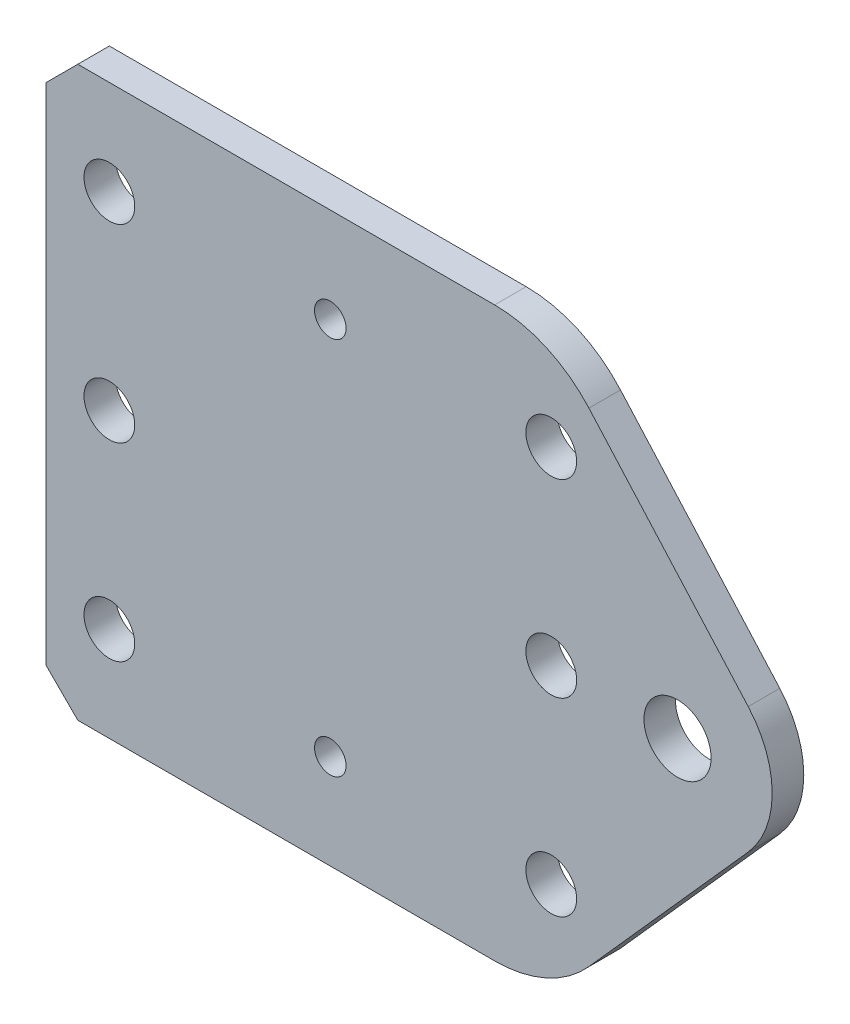
SolidWorks part; units mm, degrees
material "6061-T6 (SS)"
ref_plane "Front Plane" through (0, 0, 0) normal (0, 0, 1) x (1, 0, 0)
ref_plane "Top Plane" through (0, 0, 0) normal (0, 1, 0) x (1, 0, 0)
ref_plane "Right Plane" through (0, 0, 0) normal (1, 0, 0) x (0, 0, -1)
sketch "Sketch1" plane through (0, 0, 0) normal (0, 0, 1) x (1, 0, 0)
  line L0 (0, 0) -> (45.1053, 0)
  line L1 (54.5881, 4.2521) -> (70.6121, 22.2391)
  line L2 (70.6121, 34.9109) -> (54.5881, 52.8979)
  line L3 (45.1053, 57.15) -> (0, 57.15)
  line L4 (0, 57.15) -> (0, 0)
  arc A0 (70.6121, 22.2391) -> (70.6121, 34.9109) centre (63.5, 28.575) ccw
  circle A1 centre (63.5, 28.575) radius 3.3782
  arc A2 (45.1053, 0) -> (54.5881, 4.2521) centre (45.1053, 12.7) ccw
  arc A3 (54.5881, 52.8979) -> (45.1053, 57.15) centre (45.1053, 44.45) ccw
  point P11 (50.8, 0)
  dimension "D3" = 12.7
  dimension "D4" = 9.525
  dimension "D5" = 6.7564
  dimension "D6" = 12.7
  dimension "D1" = 57.15
  dimension "D2" = 50.8
extrude "Boss-Extrude1" add sketch "Sketch1" along normal blind 3.175
hole_wizard "#10 Clearance Hole1" positions "Sketch2" profile "Sketch3" hole size "#10" standard "ANSI Inch" end condition through all
sketch "Sketch2" plane through (0, 0, 3.175) normal (0, 0, 1) x (1, 0, 0)
  line L13 (0, 57.15) -> (0, 0) construction
  circle A0 centre (63.5, 28.575) radius 3.3782 construction
  circle A1 centre (63.5, 28.575) radius 3.3782
  point P0 (50.8, 28.575)
  point P2 (6.35, 28.575)
  point P4 (6.35, 47.625)
  point P6 (50.8, 47.625)
  point P8 (50.8, 9.525)
  point P10 (6.35, 9.525)
  dimension "D1" = 44.45
  dimension "D2" = 19.05
  dimension "D3" = 19.05
  dimension "D4" = 6.35
sketch "Sketch3" plane through (50.8, 28.575, 3.175) normal (1, 0, 0) x (0, -1, 0)
  line L0 (0, 0) -> (0, 3.175)
  line L1 (0, 3.175) -> (2.5527, 3.175)
  line L2 (2.5527, 3.175) -> (2.5527, 0)
  line L5 (2.5527, 0) -> (0, 0)
  line L11 (0, -6.35) -> (0, 107.95) construction
  dimension "Thru Hole Dia." = 5.1054
  dimension "Thru Hole Depth" = 3.175
chamfer "Chamfer1" distance 3.175 angle 45 2 edges at (0, 0, 1.5875) (0, 57.15, 1.5875)
sketch "Sketch4" plane through (0, 0, 3.175) normal (0, 0, 1) x (1, 0, 0)
  line L0 (28.575, 47.625) -> (6.35, 28.575) construction
  line L1 (6.35, 28.575) -> (28.575, 9.525) construction
  line L2 (28.575, 9.525) -> (50.8, 28.575) construction
  line L3 (50.8, 28.575) -> (28.575, 47.625) construction
  circle A0 centre (28.575, 47.625) radius 1.5875
  circle A1 centre (28.575, 9.525) radius 1.5875
  dimension "D1" = 3.175
  dimension "D2" = 38.1
extrude "Cut-Extrude1" cut sketch "Sketch4" against normal through all
